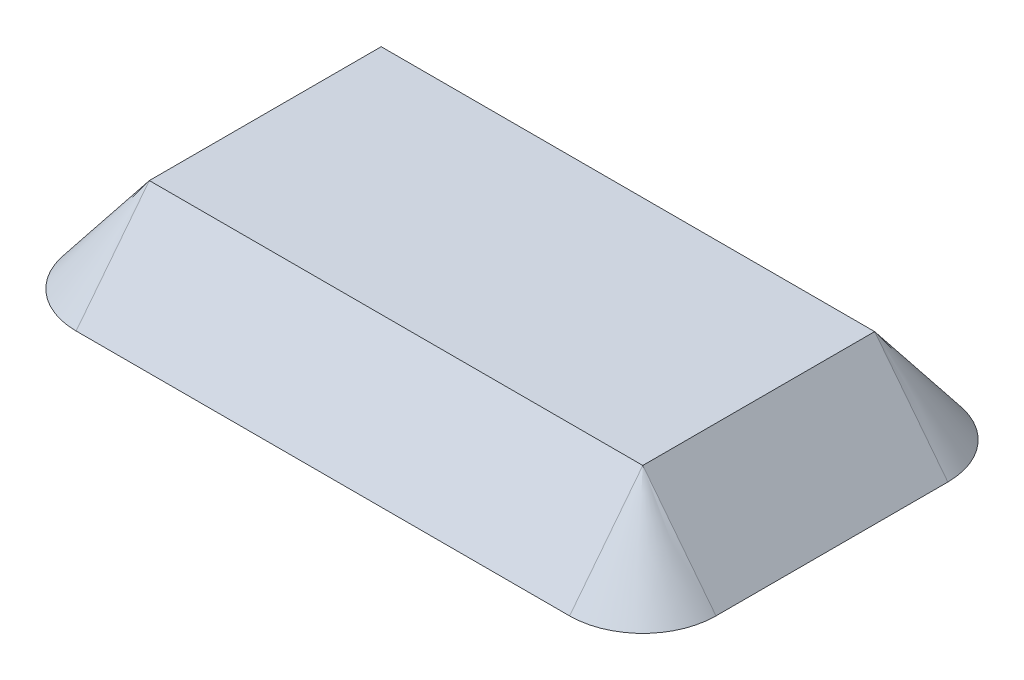
SolidWorks part; units mm, degrees
ref_plane "Alzado" through (0, 0, 0) normal (0, 0, 1) x (1, 0, 0)
ref_plane "Planta" through (0, 0, 0) normal (0, 1, 0) x (1, 0, 0)
ref_plane "Vista lateral" through (0, 0, 0) normal (1, 0, 0) x (0, 0, -1)
sketch "Croquis1" plane through (0, 0, 0) normal (0, 1, 0) x (1, 0, 0)
  line L1 (102.25, 47.25) -> (-102.25, 47.25)
  line L2 (102.25, 47.25) -> (102.25, -47.25)
  line L3 (102.25, -47.25) -> (-102.25, -47.25)
  line L4 (-102.25, 47.25) -> (-102.25, -47.25)
  line L5 (102.25, 47.25) -> (-102.25, -47.25) construction
  line L6 (102.25, -47.25) -> (-102.25, 47.25) construction
  line L7 (103.75, 48.75) -> (-103.75, 48.75)
  line L8 (103.75, 48.75) -> (103.75, -48.75)
  line L9 (103.75, -48.75) -> (-103.75, -48.75)
  line L10 (-103.75, 48.75) -> (-103.75, -48.75)
  line L11 (103.75, 48.75) -> (-103.75, -48.75) construction
  line L12 (103.75, -48.75) -> (-103.75, 48.75) construction
  point P0 (0, 0)
  point P6 (0, 0)
extrude "Saliente-Extruir1" add sketch "Croquis1" along normal blind 25
sketch "Croquis2" plane through (0, 25, 0) normal (0, 1, 0) x (1, 0, 0)
  line L1 (-103.75, -48.75) -> (103.75, -48.75)
  line L2 (-103.75, -48.75) -> (-103.75, 48.75)
  line L3 (-103.75, 48.75) -> (103.75, 48.75)
  line L4 (103.75, -48.75) -> (103.75, 48.75)
extrude "Saliente-Extruir2" add sketch "Croquis2" along normal blind 3
sketch "Croquis3" plane through (-103.75, 0, 0) normal (-1, 0, 0) x (0, 0, 1)
  line L0 (48.75, 28) -> (79.5331, -11.4005)
  line L1 (48.75, 28) -> (48.75, 0) construction
  line L2 (0, 28) -> (0, 0) construction
  line L3 (-48.75, 28) -> (48.75, 28) construction
  line L4 (-48.75, 28) -> (-79.5331, -11.4005)
  line L5 (-79.5331, -11.4005) -> (-78.0331, -11.4005)
  line L6 (-48.75, 26.0801) -> (-78.0331, -11.4005)
  line L7 (-48.75, 28) -> (-48.75, 26.0801)
  line L8 (79.5331, -11.4005) -> (78.0331, -11.4005)
  line L9 (48.75, 26.0801) -> (78.0331, -11.4005)
  line L10 (48.75, 28) -> (48.75, 26.0801)
  dimension "D1" = 38
extrude "Saliente-Extruir3" add sketch "Croquis3" against normal up to surface (207.5 mm away) up to face at (103.75, 14, 0)
sketch "Croquis4" plane through (0, 0, 48.75) normal (0, 0, 1) x (1, 0, 0)
  line L0 (-103.75, 28) -> (-134.5331, -11.4005)
  line L1 (-103.75, 26.0801) -> (-103.75, 0) construction
  line L2 (-134.5331, -11.4005) -> (-133.0331, -11.4005)
  line L3 (-133.0331, -11.4005) -> (-102.25, 28)
  line L4 (-103.75, 28) -> (-102.25, 28)
  line L5 (-103.75, 28) -> (103.75, 28) construction
  dimension "D1" = 38
extrude "Saliente-Extruir4" add sketch "Croquis4" against normal up to surface (97.5 mm away) up to face at (0, 13.04, -48.75)
sketch "Croquis5" plane through (0, 0, 48.75) normal (0, 0, 1) x (1, 0, 0)
  line L0 (-103.75, 28) -> (-134.5331, -11.4005)
  line L1 (-134.5331, -11.4005) -> (-133.0331, -11.4005)
  line L2 (-133.0331, -11.4005) -> (-103.75, 26.0801)
  line L3 (-103.75, 26.0801) -> (-103.75, 28)
revolve "Revolución1" add sketch "Croquis5" angle 90 about L3
sketch "Croquis6" plane through (-103.75, 0, 0) normal (-1, 0, 0) x (0, 0, 1)
  line L0 (-48.75, 28) -> (-79.5331, -11.4005)
  line L1 (-79.5331, -11.4005) -> (-78.0331, -11.4005)
  line L2 (-78.0331, -11.4005) -> (-48.75, 26.0801)
  line L3 (-48.75, 26.0801) -> (-48.75, 28)
revolve "Revolución2" add sketch "Croquis6" angle 90 about L3
sketch "Croquis7" plane through (103.75, 0, 0) normal (1, 0, 0) x (0, 0, -1)
  line L0 (48.75, 26.0801) -> (48.75, 28)
  line L1 (48.75, 28) -> (79.5331, -11.4005)
  line L2 (79.5331, -11.4005) -> (78.0331, -11.4005)
  line L3 (78.0331, -11.4005) -> (48.75, 26.0801)
revolve "Revolución3" add sketch "Croquis7" angle 90
sketch "Croquis8" plane through (103.75, 0, 0) normal (1, 0, 0) x (0, 0, -1)
  line L0 (-48.75, 28) -> (-79.5331, -11.4005)
  line L1 (-79.5331, -11.4005) -> (-78.0331, -11.4005)
  line L2 (-78.0331, -11.4005) -> (-48.75, 26.0801)
  line L3 (-48.75, 26.0801) -> (-48.75, 28)
revolve "Revolución4" add sketch "Croquis8" angle 90 about L3
sketch "Croquis9" plane through (0, 0, 48.75) normal (0, 0, -1) x (-1, 0, 0)
  line L0 (-103.75, 28) -> (-103.75, 26.0801)
  line L1 (-103.75, 26.0801) -> (-133.0331, -11.4005)
  line L4 (-133.0331, -11.4005) -> (-134.5331, -11.4005)
  line L5 (-134.5331, -11.4005) -> (-103.75, 28)
extrude "Saliente-Extruir5" add sketch "Croquis9" along normal up to surface (97.5 mm away) up to face at (118.7665, 7.8198, -48.75)
sketch "Croquis10" plane through (102.25, 0, 0) normal (-1, 0, 0) x (0, 0, 1)
  line L0 (0, 0) -> (0, 6)
  line L1 (47.25, 0) -> (-47.25, 0) construction
  line L3 (47.25, 25) -> (47.25, 0) construction
  line L4 (47.25, 25) -> (-47.25, 25) construction
  line L5 (47.25, 6) -> (44.75, 6)
  line L6 (47.25, 6) -> (47.25, 25)
  line L7 (47.25, 25) -> (44.75, 25)
  line L8 (44.75, 6) -> (44.75, 25)
  line M6 (47.25, 0) -> (47.25, 25)
  line M7 (47.25, 25) -> (-47.25, 25)
extrude "Saliente-Extruir6" add sketch "Croquis10" along normal up to surface (204.5 mm away) contours L8 L5 M6 M7 up to face at (-102.25, 12.5, 0)
sketch "Croquis11" plane through (102.25, 0, 0) normal (-1, 0, 0) x (0, 0, 1)
  line L0 (0, 0) -> (0, 6)
  line L1 (47.25, 0) -> (-47.25, 0) construction
  line L3 (-47.25, 25) -> (-47.25, 0) construction
  line L4 (44.75, 25) -> (-47.25, 25) construction
  line L5 (-47.25, 6) -> (-44.75, 6)
  line L6 (-47.25, 6) -> (-47.25, 25)
  line L7 (-47.25, 25) -> (-44.75, 25)
  line L8 (-44.75, 6) -> (-44.75, 25)
  line M8 (44.75, 25) -> (-47.25, 25)
  line M9 (-47.25, 25) -> (-47.25, 0)
extrude "Saliente-Extruir7" add sketch "Croquis11" along normal up to surface (204.5 mm away) contours L5 L8 M8 M9 up to face at (-102.25, 10.3333, 14.9167)
sketch "Croquis12" plane through (0, 0, 47.25) normal (0, 0, -1) x (-1, 0, 0)
  line L0 (-102.25, 0) -> (102.25, 0)
sketch "Croquis13" plane through (-102.25, 0, 0) normal (1, 0, 0) x (0, 0, -1)
  line L0 (0, 0) -> (0, -10)
  line L1 (47.25, 0) -> (-47.25, 0) construction
  circle A0 centre (0, -10) radius 10
extrude "Saliente-Extruir8" add sketch "Croquis13" along normal blind 0.3 separate body contours A0
sketch "Croquis14" plane through (-102.25, 0, 0) normal (-1, 0, 0) x (0, 0, 1)
  circle A0 centre (0, -10) radius 10
extrude "Saliente-Extruir9" add sketch "Croquis14" along normal up to surface (1.5 mm away) up to face at (-103.75, 13.04, 0)
sketch "Croquis15" plane through (-103.75, 0, 0) normal (-1, 0, 0) x (0, 0, 1)
  line L1 (-10, 10) -> (10, 10)
  line L2 (-10, 10) -> (-10, -10)
  line L3 (-10, -10) -> (10, -10)
  line L4 (10, 10) -> (10, -10)
  line L5 (-10, 10) -> (10, -10) construction
  line L6 (-10, -10) -> (10, 10) construction
  circle A0 centre (0, -10) radius 10 construction
  point P0 (0, 0)
extrude "Saliente-Extruir10" add sketch "Croquis15" against normal up to surface (1.5 mm away) up to face at (-102.25, 8.2222, 0)
sketch "Croquis16" plane through (102.25, 0, 0) normal (-1, 0, 0) x (0, 0, 1)
  line L0 (0, 0) -> (0, -10)
  line L1 (47.25, 0) -> (-47.25, 0) construction
  line L3 (-10, 10) -> (10, 10)
  line L4 (-10, 10) -> (-10, -10)
  line L5 (-10, -10) -> (10, -10)
  line L6 (10, 10) -> (10, -10)
  line L7 (-10, 10) -> (10, -10) construction
  line L8 (-10, -10) -> (10, 10) construction
  circle A0 centre (0, -10) radius 10
  line M5 (-47.25, 0) -> (47.25, 0)
extrude "Saliente-Extruir11" add sketch "Croquis16" against normal up to surface (1.5 mm away) contours L5 A0 | L5 A0 L0 | L0 A0 L5 | A0 L4 M5 | A0 L6 M5 | L6 L3 L4 M5 up to face at (103.75, 13.04, 0)
sketch "Croquis17" plane through (102.25, 0, 0) normal (-1, 0, 0) x (0, 0, 1)
  circle A0 centre (0, -10) radius 10
extrude "Saliente-Extruir12" add sketch "Croquis17" along normal blind 0.3
sketch "Croquis18" plane through (101.95, 0, 0) normal (-1, 0, 0) x (0, 0, 1)
  circle A0 centre (0, -10) radius 10
extrude "Saliente-Extruir13" add sketch "Croquis18" along normal blind 1.5
sketch "Croquis19" plane through (-101.95, 0, 0) normal (1, 0, 0) x (0, 0, -1)
  circle A0 centre (0, -10) radius 10
extrude "Saliente-Extruir14" add sketch "Croquis19" along normal blind 1.5
